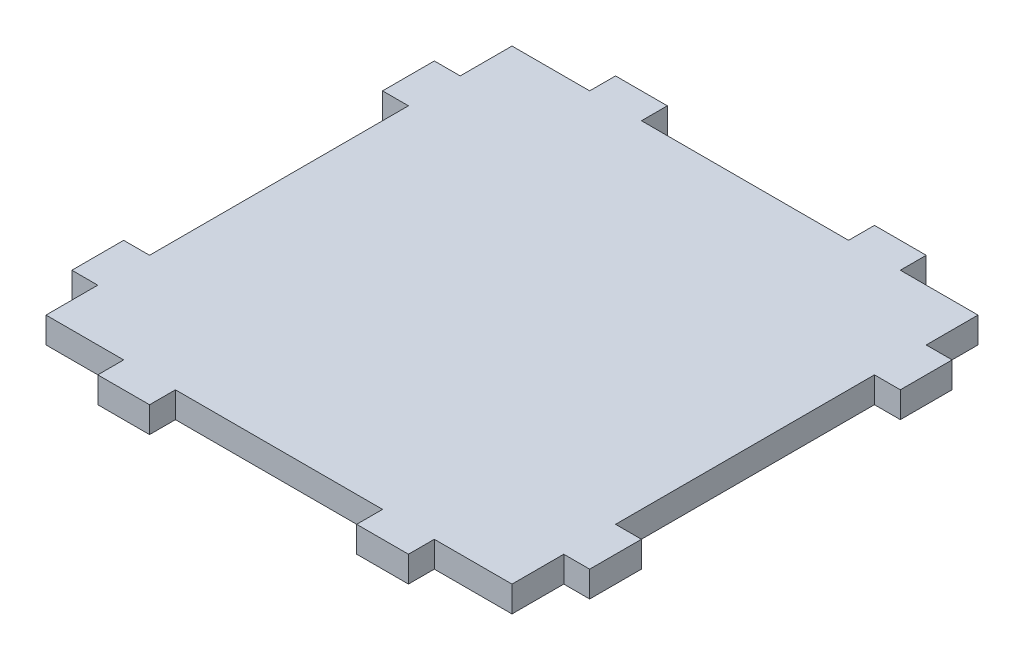
SolidWorks part; units mm, degrees
ref_plane "Front Plane" through (0, 0, 0) normal (0, 0, 1) x (1, 0, 0)
ref_plane "Top Plane" through (0, 0, 0) normal (0, 1, 0) x (1, 0, 0)
ref_plane "Right Plane" through (0, 0, 0) normal (1, 0, 0) x (0, 0, -1)
sketch "Sketch1" plane through (0, 0, 0) normal (0, 1, 0) x (1, 0, 0)
  line L0 (0, -1000) -> (0, 49000) construction
  line L1 (-45, 45) -> (-30, 45)
  line L2 (-45, 45) -> (-45, 35)
  line L3 (-45, -45) -> (0, -45) construction
  line L4 (45, 0) -> (45, -45) construction
  line L5 (-45, 45) -> (45, -45) construction
  line L6 (-45, -45) -> (45, 45) construction
  line L7 (-30, 45) -> (-20, 45) construction
  line L8 (-30, 45) -> (-30, 50)
  line L9 (-30, 50) -> (-20, 50)
  line L10 (-20, 45) -> (-20, 50)
  line L11 (-1000, 0) -> (49000, 0) construction
  line L12 (-30, 45) -> (-20, 45) construction
  line L13 (-20, 45) -> (20, 45)
  line L14 (-45, 35) -> (-45, 25) construction
  line L15 (-45, 35) -> (-50, 35)
  line L16 (-45, 35) -> (-45, 25) construction
  line L17 (-45, 25) -> (-50, 25)
  line L18 (-50, 35) -> (-50, 25)
  line L19 (-45, 25) -> (-45, -25)
  line L20 (0, 45) -> (45, 45) construction
  line L21 (45, 45) -> (45, -45) construction
  line L22 (0, -45) -> (45, -45) construction
  line L23 (-45, 0) -> (-45, -45) construction
  line L24 (45, 25) -> (45, -25)
  line L25 (45, 45) -> (45, 35)
  line L26 (45, 25) -> (50, 25)
  line L27 (45, 35) -> (50, 35)
  line L28 (50, 35) -> (50, 25)
  line L29 (20, 45) -> (20, 50)
  line L30 (45, 45) -> (30, 45)
  line L31 (30, 45) -> (30, 50)
  line L32 (30, 50) -> (20, 50)
  line L33 (0, -45) -> (45, -45) construction
  line L34 (-45, -35) -> (-45, -25) construction
  line L35 (-45, -35) -> (-45, -25) construction
  line L36 (-30, -45) -> (-20, -45) construction
  line L37 (-30, -45) -> (-20, -45) construction
  line L38 (30, -50) -> (20, -50)
  line L39 (30, -45) -> (30, -50)
  line L40 (45, -45) -> (30, -45)
  line L41 (20, -45) -> (20, -50)
  line L42 (50, -35) -> (50, -25)
  line L43 (45, -35) -> (50, -35)
  line L44 (45, -25) -> (50, -25)
  line L45 (45, -45) -> (45, -35)
  line L46 (-50, -35) -> (-50, -25)
  line L47 (-45, -25) -> (-50, -25)
  line L48 (-45, -35) -> (-50, -35)
  line L49 (-20, -45) -> (20, -45)
  line L50 (-20, -45) -> (-20, -50)
  line L51 (-30, -50) -> (-20, -50)
  line L52 (-30, -45) -> (-30, -50)
  line L53 (-45, -45) -> (-45, -35)
  line L54 (-45, -45) -> (-30, -45)
  point P0 (0, 0)
  dimension "D1" = 90
  dimension "D2" = 90
  dimension "D3" = 10
  dimension "D4" = 5
  dimension "D5" = 15
  dimension "D6" = 10
  dimension "D7" = 10
  dimension "D8" = 5
extrude "Boss-Extrude1" add sketch "Sketch1" along normal blind 5
